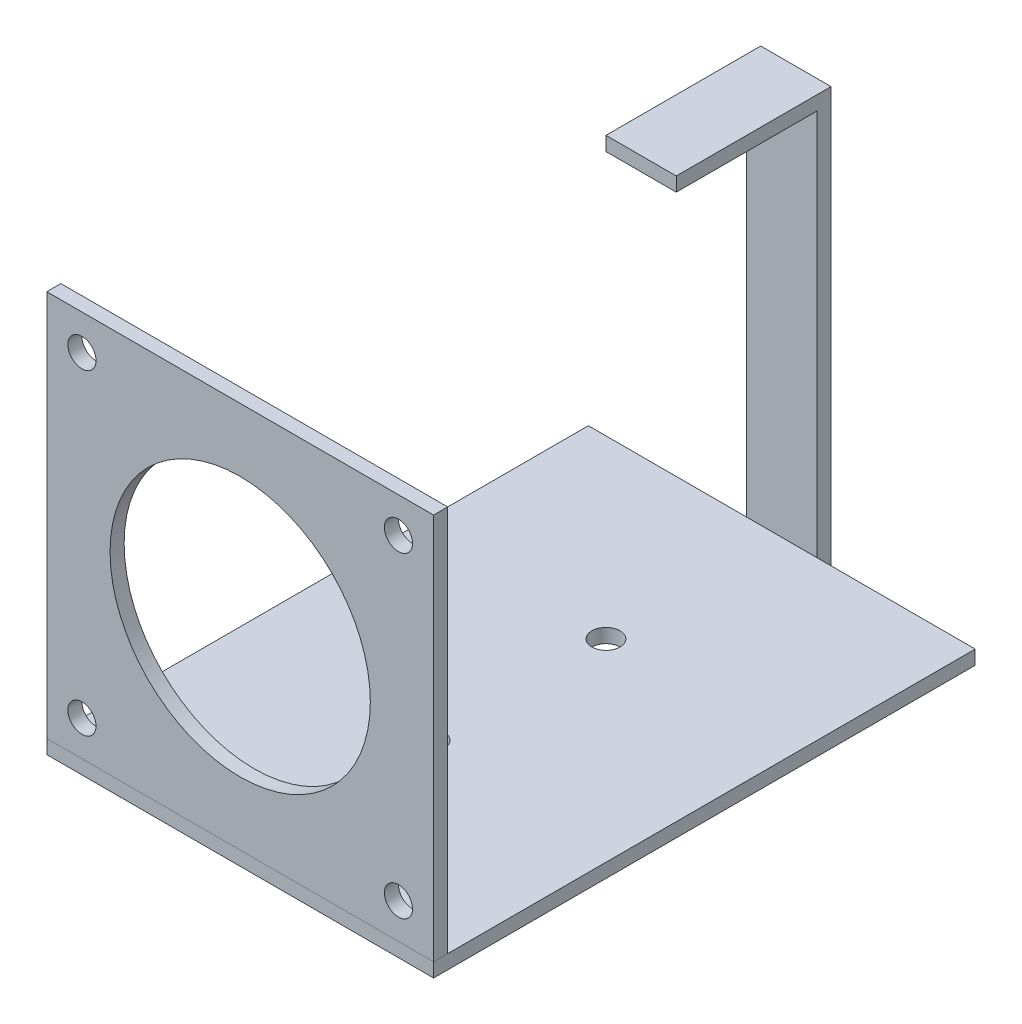
SolidWorks part; units mm, degrees
ref_plane "Front Plane" through (0, 0, 0) normal (0, 0, 1) x (1, 0, 0)
ref_plane "Top Plane" through (0, 0, 0) normal (0, 1, 0) x (1, 0, 0)
ref_plane "Right Plane" through (0, 0, 0) normal (1, 0, 0) x (0, 0, -1)
sketch "Sketch1" plane through (0, 0, 0) normal (0, 0, 1) x (1, 0, 0)
  line L1 (-27.5, 27.5) -> (27.5, 27.5)
  line L2 (-27.5, 27.5) -> (-27.5, -27.5)
  line L3 (-27.5, -27.5) -> (27.5, -27.5)
  line L4 (27.5, 27.5) -> (27.5, -27.5)
  circle A0 centre (-22.5, 22.5) radius 2
  circle A1 centre (22.5, 22.5) radius 2
  circle A2 centre (-22.5, -22.5) radius 2
  circle A3 centre (22.5, -22.5) radius 2
  circle A4 centre (0, 0) radius 18.5
  dimension "D5" = 4
  dimension "D6" = 4
  dimension "D7" = 4
  dimension "D8" = 4
  dimension "D17" = 37
  dimension "D1" = 55
  dimension "D2" = 55
  dimension "D3" = 27.5
  dimension "D4" = 27.5
  dimension "D9" = 5
  dimension "D10" = 5
  dimension "D11" = 5
  dimension "D12" = 5
  dimension "D13" = 5
  dimension "D14" = 5
  dimension "D15" = 5
  dimension "D16" = 5
extrude "Boss-Extrude1" add sketch "Sketch1" along normal blind 2
sketch "Sketch2" plane through (27.5, 0, 0) normal (1, 0, 0) x (0, 0, -1)
  line L0 (0, -27.5) -> (75, -27.5)
  line L1 (-2, -27.5) -> (-2, -29.5)
  line L2 (-2, -29.5) -> (75, -29.5)
  line L3 (75, -29.5) -> (75, -27.5)
  line L4 (-2, -27.5) -> (0, -27.5)
  dimension "D1" = 75
  dimension "D2" = 2
extrude "Boss-Extrude2" add sketch "Sketch2" against normal blind 55 separate body
sketch "Sketch3" plane through (0, 0, -75) normal (0, 0, -1) x (-1, 0, 0)
  line L0 (0, -29.5) -> (-5, -29.5)
  line L4 (27.5, -29.5) -> (-27.5, -29.5) construction
  line L5 (-5, -29.5) -> (-5, 27.5)
  line L6 (-5, 27.5) -> (5, 27.5)
  line L7 (5, 27.5) -> (5, -29.5)
  line L9 (5, -29.5) -> (0, -29.5)
  dimension "D1" = 5
  dimension "D2" = 5
  dimension "D3" = 57
extrude "Boss-Extrude3" add sketch "Sketch3" along normal blind 2
sketch "Sketch4" plane through (0, 27.5, 0) normal (0, 1, 0) x (1, 0, 0)
  line L0 (-5, 77) -> (-5, 55)
  line L1 (-5, 55) -> (5, 55)
  line L2 (5, 55) -> (5, 77)
  line L3 (5, 77) -> (-5, 77)
  dimension "D1" = 22
  dimension "D2" = 10
extrude "Boss-Extrude4" add sketch "Sketch4" along normal blind 2
sketch "Sketch5" plane through (0, -29.5, 0) normal (0, -1, 0) x (1, 0, 0)
  line L0 (0, 0) -> (0, -25) construction
  line L1 (0, -25) -> (0, -50) construction
  circle A0 centre (0, -25) radius 2
  circle A1 centre (0, -50) radius 2
  dimension "D3" = 4
  dimension "D4" = 4
  dimension "D1" = 25
  dimension "D2" = 25
extrude "Cut-Extrude1" cut sketch "Sketch5" against normal blind 2
